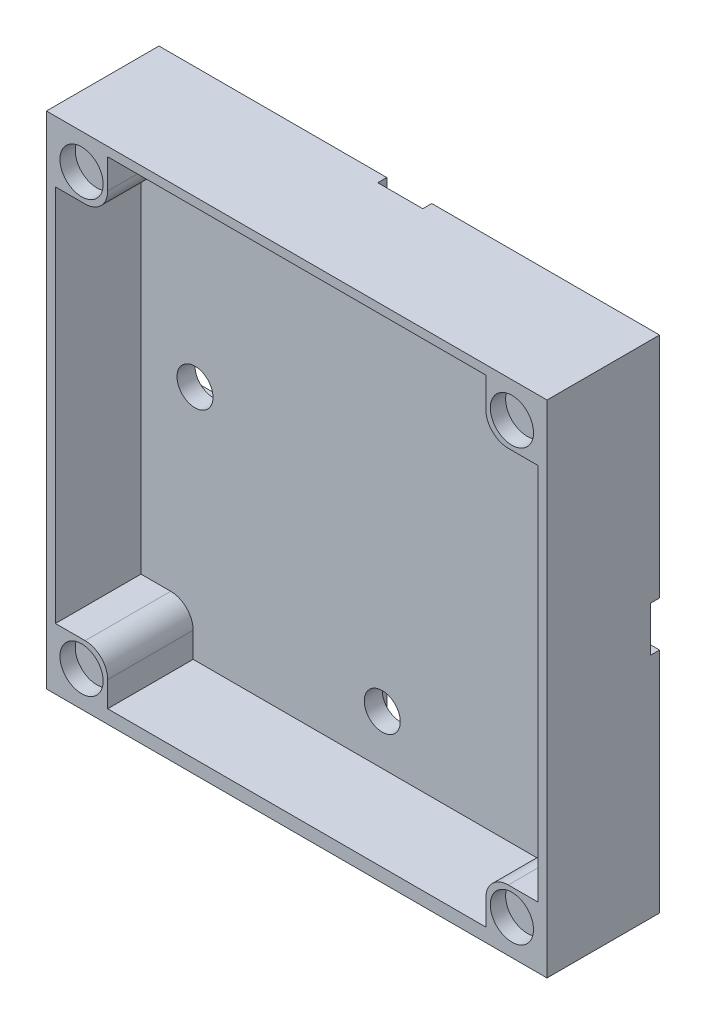
SolidWorks part; units mm, degrees
ref_plane "Přední rovina" through (0, 0, 0) normal (0, 0, 1) x (1, 0, 0)
ref_plane "Horní rovina" through (0, 0, 0) normal (0, 1, 0) x (1, 0, 0)
ref_plane "Pravá rovina" through (0, 0, 0) normal (1, 0, 0) x (0, 0, -1)
sketch "Skica1" plane through (0, 0, 0) normal (0, 0, 1) x (1, 0, 0)
  line L1 (27.8, 27.8) -> (-27.8, 27.8)
  line L2 (27.8, 27.8) -> (27.8, -27.8)
  line L3 (27.8, -27.8) -> (-27.8, -27.8)
  line L4 (-27.8, 27.8) -> (-27.8, -27.8)
  line L5 (27.8, 27.8) -> (-27.8, -27.8) construction
  line L6 (27.8, -27.8) -> (-27.8, 27.8) construction
  point P0 (0, 0)
  point P5 (-27.5, 0)
  point P11 (4.5, 0)
  dimension "D1" = 55.6
  dimension "D2" = 55.6
extrude "Přidat vysunutím2" add sketch "Skica1" along normal blind 3 contours L2 L1 L4 L3
sketch "Skica5" plane through (0, 0, 0) normal (0, 0, -1) x (-1, 0, 0)
  line L0 (2.5, 27.8) -> (-2.5, 27.8)
  line L5 (2.5, 27.8) -> (2.5, -27.8)
  line L10 (27.8, 27.8) -> (27.8, -27.8) construction
  line L11 (-27.8, 2.5) -> (27.8, 2.5)
  line L12 (-27.8, 2.5) -> (-27.8, -2.5)
  line L13 (-27.8, -2.5) -> (27.8, -2.5)
  line L14 (27.8, 2.5) -> (27.8, -2.5)
  line L15 (-27.8, 2.5) -> (27.8, -2.5) construction
  line L16 (-27.8, -2.5) -> (27.8, 2.5) construction
  line L17 (2.5, -27.8) -> (-2.5, -27.8)
  line L18 (-2.5, 27.8) -> (-2.5, -27.8)
  line L19 (27.8, -2.5) -> (27.8, 2.5)
  line L20 (27.8, -2.5) -> (-27.8, -2.5)
  line L21 (-27.8, -2.5) -> (-27.8, 2.5)
  line L22 (27.8, 2.5) -> (-27.8, 2.5)
  line L23 (-2.5, -27.8) -> (2.5, -27.8)
  line L24 (-2.5, -27.8) -> (-2.5, 27.8)
  line L25 (-2.5, 27.8) -> (2.5, 27.8)
  line L26 (2.5, -27.8) -> (2.5, 27.8)
  point P0 (0, 0)
  point P23 (0, 0)
  dimension "D1" = 5
  dimension "D2" = 4
extrude "Odebrat vysunutím3" cut sketch "Skica5" against normal blind 1 contours L11 L14 L13 L12 | L0 L18 L17 L5
sketch "Skica14" plane through (0, 0, 3) normal (0, 0, 1) x (1, 0, 0)
  line L1 (-27.8, 27.8) -> (27.8, 27.8)
  line L2 (-27.8, 27.8) -> (-27.8, -27.8)
  line L3 (-27.8, -27.8) -> (27.8, -27.8)
  line L4 (27.8, 27.8) -> (27.8, -27.8)
  line L5 (-26.8, 26.8) -> (26.8, 26.8)
  line L6 (-26.8, 26.8) -> (-26.8, -27.8)
  line L7 (-26.8, -27.8) -> (26.8, -27.8)
  line L8 (26.8, 26.8) -> (26.8, -27.8)
  line L9 (-26.8, -27.8) -> (26.8, -27.8)
  line L10 (-26.8, -27.8) -> (-26.8, -26.8)
  line L12 (26.8, -27.8) -> (26.8, -26.3)
  line L13 (-26.8, -27.8) -> (26.8, -27.8)
  line L14 (-26.8, -27.8) -> (-26.8, -26.3)
  line L15 (-26.8, -26.3) -> (26.8, -26.3)
  line L16 (26.8, -27.8) -> (26.8, -26.3)
  line M13 (-27.8, -27.8) -> (27.8, -27.8)
  line M14 (27.8, -27.8) -> (27.8, 27.8)
  line M15 (27.8, 27.8) -> (-27.8, 27.8)
  line M16 (-27.8, 27.8) -> (-27.8, -27.8)
  dimension "D1" = 1
  dimension "D2" = 1
  dimension "D3" = 1
  dimension "D4" = 0
  dimension "D5" = 1
  dimension "D6" = 53.6
extrude "Přidat vysunutím9" add sketch "Skica14" along normal blind 9.5 contours L5 L8 L6 M13 M14 M15 M16 | L14 L13 L16 L15
sketch "Skica17" plane through (0, 0, 1) normal (0, 0, -1) x (-1, 0, 0)
  line L0 (-27.8, 2.5) -> (-27.8, -2.5) construction
  line L2 (27.8, 2.5) -> (27.8, -2.5) construction
  circle A0 centre (-20.8, 0) radius 2
  circle A1 centre (20.8, 0) radius 2
  circle A2 centre (0, 20.8) radius 2
  circle A3 centre (0, -20.8) radius 2
  circle A4 centre (20.8, 0) radius 2
  circle A5 centre (-20.8, 0) radius 2
  circle A6 centre (0, -20.8) radius 2
  circle A7 centre (0, 20.8) radius 2
  point P23 (0, 0)
  dimension "D1" = 4
  dimension "D2" = 4
  dimension "D3" = 7
  dimension "D4" = 4
  dimension "D5" = 7
extrude "Odebrat vysunutím8" cut sketch "Skica17" against normal blind 4 contours A1 | A0 | A2 | A3
sketch "Skica19" plane through (0, 0, 0) normal (0, 0, -1) x (-1, 0, 0)
  line L1 (-27.8, 27.8) -> (-21, 27.8)
  line L2 (-27.8, 27.8) -> (-27.8, 21)
  line L3 (-27.8, 21) -> (-21, 21)
  line L4 (-21, 27.8) -> (-21, 21)
  line L5 (27.8, 27.8) -> (21, 27.8)
  line L6 (27.8, 27.8) -> (27.8, 21)
  line L7 (27.8, 21) -> (21, 21)
  line L8 (21, 27.8) -> (21, 21)
  line L9 (-27.8, -27.8) -> (-21, -27.8)
  line L10 (-27.8, -27.8) -> (-27.8, -21)
  line L11 (-27.8, -21) -> (-21, -21)
  line L12 (-21, -27.8) -> (-21, -21)
  line L13 (27.8, -27.8) -> (21, -27.8)
  line L14 (27.8, -27.8) -> (27.8, -21)
  line L15 (27.8, -21) -> (21, -21)
  line L16 (21, -27.8) -> (21, -21)
  dimension "D1" = 6.8
  dimension "D2" = 6.8
  dimension "D3" = 6.8
  dimension "D4" = 6.8
extrude "Přidat vysunutím10" add sketch "Skica19" against normal blind 12.5
sketch "Skica20" plane through (0, 0, 12.5) normal (0, 0, 1) x (1, 0, 0)
  line L0 (-27.8, -27.8) -> (27.8, -27.8) construction
  line L2 (-27.8, 27.8) -> (-27.8, -27.8) construction
  line L3 (27.8, 27.8) -> (-27.8, 27.8) construction
  line L4 (27.8, -27.8) -> (27.8, 27.8) construction
  line L5 (-27.8, -27.8) -> (27.8, -27.8) construction
  circle A0 centre (-23.9, -23.9) radius 2.4
  circle A1 centre (-23.9, 23.9) radius 2.4
  circle A2 centre (23.9003, 23.9) radius 2.4
  circle A3 centre (23.9003, -23.9) radius 2.4
  dimension "D1" = 4.8
  dimension "D4" = 4.8
  dimension "D5" = 3.9
  dimension "D7" = 4.8
  dimension "D10" = 4.8
  dimension "D2" = 3.9
  dimension "D3" = 3.9
  dimension "D6" = 3.9
  dimension "D8" = 3.8997
  dimension "D9" = 3.9
  dimension "D11" = 3.9
  dimension "D12" = 3.8997
extrude "Odebrat vysunutím9" cut sketch "Skica20" against normal blind 1.7
fillet "Zaoblit1" radius 2.5 4 edges at (21, 21, 7.75) (21, -21, 7.75) (-21, -21, 7.75) (-21, 21, 7.75)
